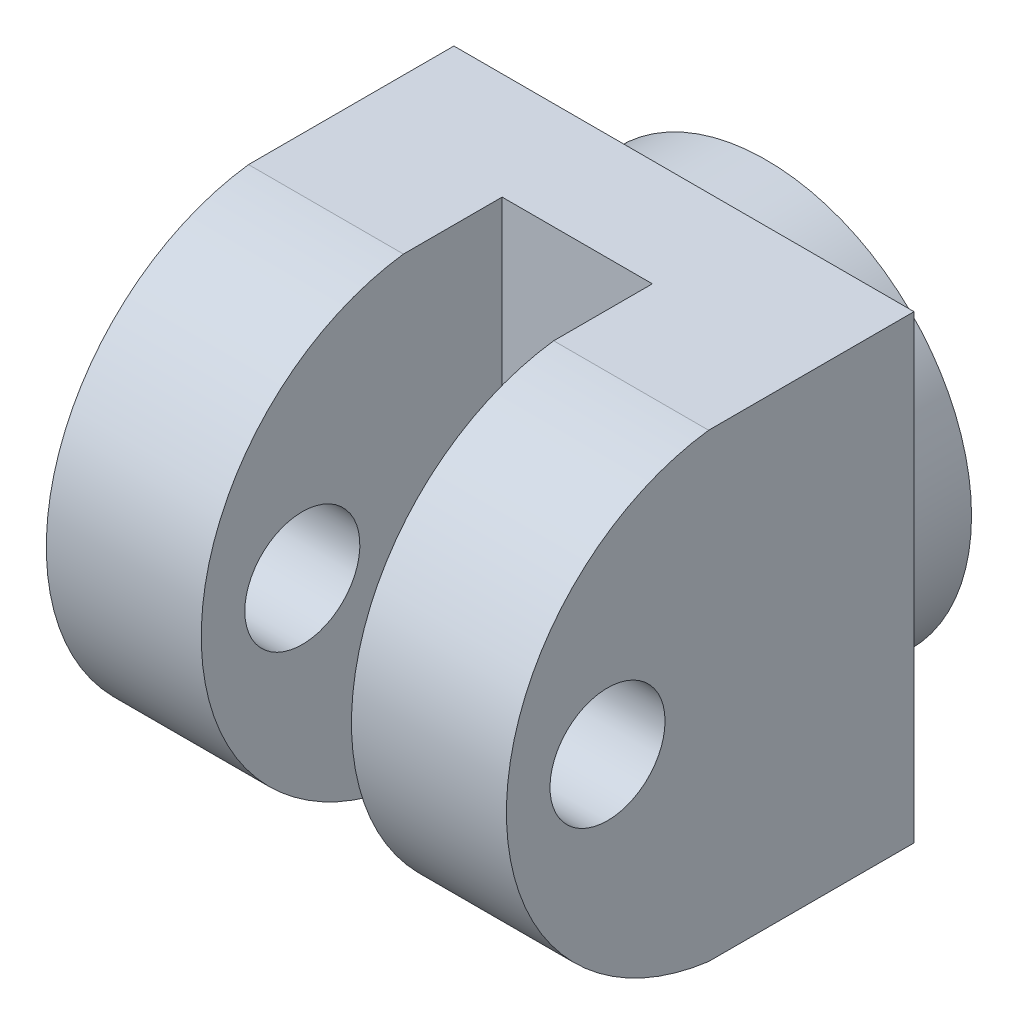
SolidWorks part; units mm, degrees
ref_plane "Front Plane" through (0, 0, 0) normal (0, 0, 1) x (1, 0, 0)
ref_plane "Top Plane" through (0, 0, 0) normal (0, 1, 0) x (1, 0, 0)
ref_plane "Right Plane" through (0, 0, 0) normal (1, 0, 0) x (0, 0, -1)
sketch "Sketch1" plane through (0, 0, 0) normal (0, 0, 1) x (1, 0, 0)
  circle A0 centre (0, 0) radius 10
  circle A1 centre (0, 0) radius 12.5
  dimension "D1" = 25
  dimension "D2" = 20
extrude "Boss-Extrude1" add sketch "Sketch1" along normal blind 5
sketch "Sketch2" plane through (0, 0, 5) normal (0, 0, 1) x (1, 0, 0)
  line L1 (-14, 14) -> (14, 14)
  line L2 (-14, 14) -> (-14, -14)
  line L3 (-14, -14) -> (14, -14)
  line L4 (14, 14) -> (14, -14)
  line L5 (-14, 14) -> (14, -14) construction
  line L6 (-14, -14) -> (14, 14) construction
  point P0 (0, 0)
  dimension "D1" = 28
  dimension "D2" = 28
extrude "Boss-Extrude2" add sketch "Sketch2" along normal blind 25
sketch "Sketch3" plane through (-14, 0, 0) normal (-1, 0, 0) x (0, 0, 1)
  line L0 (30, 14) -> (5, 14) construction
  line L1 (30, -14) -> (5, -14) construction
  line L3 (17.5, 14) -> (30, 14)
  line L4 (30, 14) -> (30, -14)
  line L5 (30, -14) -> (17.5, -14)
  arc A1 (17.5, 14) -> (17.5, -14) centre (15.6879, 0) cw
extrude "Cut-Extrude1" cut sketch "Sketch3" against normal through all
sketch "Sketch5" plane through (0, -14, 0) normal (0, -1, 0) x (1, 0, 0)
  line L0 (0, 0) -> (0, 30.3929) construction
sketch "Sketch6" plane through (0, -14, 0) normal (0, -1, 0) x (1, 0, 0)
  line L0 (-14, 11.4951) -> (14, 11.4951) construction
  line L1 (-14, 17.5) -> (-14, 5) construction
  line L2 (14, 17.5) -> (14, 5) construction
sketch "Sketch7" plane through (0, -14, 0) normal (0, -1, 0) x (1, 0, 0)
  line L0 (0, 0) -> (0, 30.3929) construction
  line L1 (-4.571, 30.9118) -> (4.571, 30.9118)
  line L2 (-4.571, 30.9118) -> (-4.571, 11.4951)
  line L3 (-4.571, 11.4951) -> (4.571, 11.4951)
  line L4 (4.571, 30.9118) -> (4.571, 11.4951)
  line L5 (-4.571, 30.9118) -> (4.571, 11.4951) construction
  line L6 (-4.571, 11.4951) -> (4.571, 30.9118) construction
  line L7 (-14, 11.4951) -> (14, 11.4951) construction
  point P0 (0, 21.2035)
extrude "Cut-Extrude2" cut sketch "Sketch7" against normal through all both and the other way through all
sketch "Sketch8" plane through (14, 0, 0) normal (1, 0, 0) x (0, 0, -1)
  line L0 (-17.5, 14) -> (-17.5, -14) construction
  line L1 (-17.5, 0) -> (-29.8047, 0) construction
  arc A0 (-17.5, 14) -> (-17.5, -14) centre (-15.6879, 0) ccw construction
  circle A1 centre (-23.6523, 0) radius 3.5
  dimension "D1" = 7
extrude "Cut-Extrude3" cut sketch "Sketch8" against normal through all both and the other way through all
